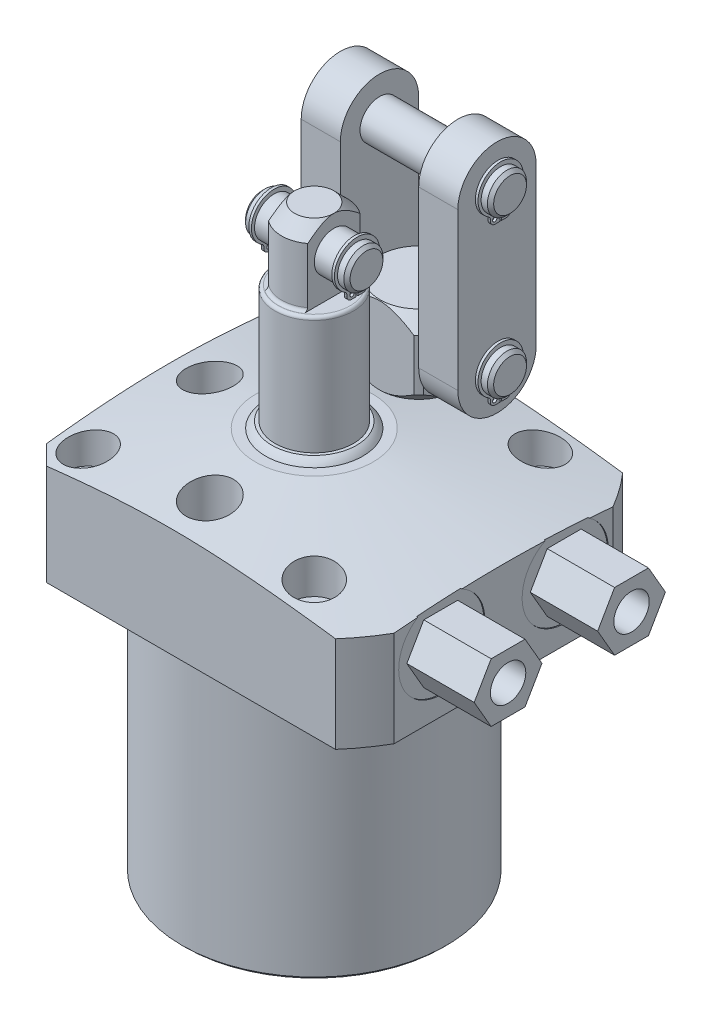
SolidWorks part; units mm, degrees
material "Alloy Steel"
ref_plane "Front Plane" through (0, 0, 0) normal (0, 0, 1) x (1, 0, 0)
ref_plane "Top Plane" through (0, 0, 0) normal (0, 1, 0) x (1, 0, 0)
ref_plane "Right Plane" through (0, 0, 0) normal (1, 0, 0) x (0, 0, -1)
sketch "Sketch28" plane through (0, 0, 0) normal (0, 0, 1) x (1, 0, 0)
  line L0 (0, 0) -> (0, 146.1857) construction
  line L1 (-14.2875, 30.1498) -> (-53.1749, 23.2929)
  line L2 (-53.1749, 23.2929) -> (-53.1749, 0)
  line L3 (-53.1749, 0) -> (-32.1437, 0)
  line L6 (-32.1437, 0) -> (-32.1437, -63.5)
  line L9 (-32.1437, -63.5) -> (0, -63.5)
  line L10 (0, -63.5) -> (0, 30.1498)
  line L11 (0, 30.1498) -> (-14.2875, 30.1498)
  dimension "D2" = 64.2874
  dimension "D3" = 63.5
  dimension "D5" = 106.3498
  dimension "D6" = 10
  dimension "D7" = 28.575
  dimension "D8" = 30.1498
revolve "Revolve7" add sketch "Sketch28" angle 360 about L0
sketch "Sketch3" plane through (0, 30.1498, 0) normal (0, 1, 0) x (-1, 0, 0)
  line L0 (34.925, -34.925) -> (-46.0248, -34.925)
  line L3 (-46.0248, 34.925) -> (34.925, 34.925)
  line L4 (34.925, -34.925) -> (34.925, 34.925)
  line L5 (-46.0248, -34.925) -> (-46.0248, 34.925)
  line L6 (-29.7523, 0) -> (31.3525, 0) construction
  dimension "D1" = 69.85
  dimension "D2" = 46.0248
  dimension "D5" = 34.925
extrude "Cut-Extrude9" cut sketch "Sketch3" against normal up to next (93.6498 mm away) flip side to cut
chamfer "Chamfer8" distance 4.7498 angle 45 2 edges at (-34.925, 11.98, -34.925) (-34.925, 11.98, 34.925)
chamfer "Chamfer5" distance 0.762 angle 45 1 edges at (0, -63.5, -32.1437)
hole_wizard "Hole1" positions "Sketch32" profile "Sketch31" legacy
sketch "Sketch32" plane through (0, 30.1498, 0) normal (0, 1, 0) x (-1, 0, 0)
  line L1 (0, 0) -> (-56.2722, 0) construction
  line L2 (0, 0) -> (0, 46.6984) construction
  point P11 (-27.4955, -27.4955)
  point P23 (-27.4955, 27.4955)
  point P25 (27.4955, -27.4955)
  point P26 (27.4955, 27.4955)
  dimension "D1" = 54.991
  dimension "D2" = 54.991
sketch "Sketch31" plane through (27.4955, 30.1498, -27.4955) normal (1, 0, 0) x (0, 0, 1)
  line L0 (0, 0) -> (0, 30.1498)
  line L1 (0, 30.1498) -> (3.5687, 30.1498)
  line L2 (3.5687, 30.1498) -> (3.5687, 11.9126)
  line L3 (3.5687, 11.9126) -> (5.5499, 11.9126)
  line L4 (5.5499, 11.9126) -> (5.5499, 0)
  line L5 (5.5499, 0) -> (0, 0)
  line L6 (0, 110) -> (0, -10) construction
  dimension "Diameter" = 7.1374
  dimension "Depth" = 30.1498
  dimension "C-Bore Diameter" = 11.0998
  dimension "C-Bore Depth" = 11.9126
sketch "Sketch34" plane through (0, 30.1498, 0) normal (0, 1, 0) x (1, 0, 0)
  line L0 (0, 0) -> (-28.6526, 0) construction
  circle A0 centre (0, 25.4) radius 5.7531
  circle A1 centre (0, -25.4) radius 5.7531
  circle A2 centre (0, 0) radius 25.4 construction
  circle A3 centre (-25.4, 0) radius 5.7531
  dimension "D1" = 11.5062
  dimension "D2" = 25.4
extrude "Cut-Extrude10" cut sketch "Sketch34" against normal blind 15.875
ref_plane "Plane23" through (0, 15.0876, 0) normal (0, -1, 0) x (1, 0, 0)
sketch "S2D0007" plane through (0, 15.0876, 0) normal (0, -1, 0) x (1, 0, 0)
  line L0 (46.0248, -15.0114) -> (46.0248, -25.4889)
  line L1 (46.0248, -25.4889) -> (45.7708, -25.4889)
  line L2 (45.7708, -25.4889) -> (45.7708, -21.228)
  line L3 (45.7708, -21.228) -> (43.7007, -20.788)
  line L4 (43.7007, -20.788) -> (42.9025, -19.9898)
  line L5 (42.9025, -19.9898) -> (31.8008, -19.9898)
  line L6 (31.8008, -19.9898) -> (28.8095, -15.0114)
  line L7 (28.8095, -15.0114) -> (46.0248, -15.0114)
  line L8 (-11.7468, -15.0114) -> (-12.1894, -15.0114) construction
  line L10 (46.0248, -26.6325) -> (46.0248, 26.6325) construction
  dimension "D1" = 12.4333
  dimension "D2" = 59
  dimension "D3" = 9.9568
  dimension "D4" = 45
  dimension "D5" = 12
  dimension "D6" = 2.0701
  dimension "D7" = 0.254
  dimension "D8" = 20.955
  dimension "D9" = 15.0114
  dimension "D10" = 13.97
revolve "Cut-Revolve2" cut sketch "S2D0007" angle 360 about L8
ref_plane "Plane24" through (0, 0, -15.0114) normal (0, 0, 1) x (1, 0, 0)
sketch "Sketch6" plane through (0, 0, -15.0114) normal (0, 0, 1) x (1, 0, 0)
  line L0 (40.0976, 0) -> (-30.1752, 0) construction
  line L1 (45.1675, 0) -> (45.1675, 1.4478)
  line L2 (45.1675, 1.4478) -> (42.1071, 1.4478)
  line L3 (40.0976, 0) -> (46.0248, 0) construction
  line L5 (39.497, 0.5588) -> (40.64, 0.5588)
  line L6 (39.497, 0) -> (45.1675, 0)
  line L8 (39.497, 0.5588) -> (39.497, 0)
  line L9 (39.497, -21.0492) -> (39.497, 0.6686) construction
  arc A1 (40.64, 0.5588) -> (42.1071, 1.4478) centre (39.497, 4.1) ccw
  dimension "D8" = 3.7211
  dimension "D1" = 1.4478
  dimension "D2" = 39.497
  dimension "D7" = 0.5588
  dimension "D9" = 11.3411
  dimension "D10" = 2.286
revolve "Cut-Revolve3" cut sketch "Sketch6" angle 360 about L9
sketch "Sketch38" plane through (45.7708, 0, 0) normal (1, 0, 0) x (0, 0, -1)
  line L1 (23.253, 15.0876) -> (19.1322, 22.225)
  line L2 (19.1322, 22.225) -> (10.8906, 22.225)
  line L3 (10.8906, 22.225) -> (6.7698, 15.0876)
  line L4 (6.7698, 15.0876) -> (10.8906, 7.9502)
  line L5 (10.8906, 7.9502) -> (19.1322, 7.9502)
  line L6 (19.1322, 7.9502) -> (23.253, 15.0876)
  circle A0 centre (15.0114, 15.0876) radius 7.1374 construction
  dimension "D1" = 14.2748
extrude "Extrude14" add sketch "Sketch38" along normal blind 16.383
hole_wizard "Hole2" positions "Sketch40" profile "Sketch39" legacy
sketch "Sketch40" plane through (62.1538, 0, 0) normal (1, 0, 0) x (0, 0, -1)
  arc A0 (10.2098, 24.4001) -> (20.8282, 23.8021) centre (15.0114, 15.0876) ccw construction
  point P0 (15.0114, 15.0876)
sketch "Sketch39" plane through (62.1538, 15.0876, -15.0114) normal (0, 1, 0) x (0, 0, -1)
  line L0 (0, 0) -> (0, 6.7056)
  line L1 (0, 6.7056) -> (4.3053, 6.7056)
  line L2 (4.3053, 6.7056) -> (4.3053, 0)
  line L3 (4.3053, 0) -> (0, 0)
  line L4 (0, 110) -> (0, -10) construction
  dimension "Diameter" = 8.6106
  dimension "Depth" = 6.7056
mirror "Mirror6" about plane through (0, 0, 0) normal (0, 0, 1) of "Hole2", "Extrude14", "Cut-Revolve2", "Cut-Revolve3"
sketch "Sketch33" plane through (0, 0, -15.0114) normal (0, 0, 1) x (1, 0, 0)
  line L0 (39.497, 8.3297) -> (39.497, -4.9597) construction
  line L1 (39.497, 2.4904) -> (39.497, -1.971) construction
  line L2 (33.8264, 1.4478) -> (45.1675, 1.4478) construction
  circle A0 centre (34.7154, 0.5842) radius 0.889
  dimension "D3" = 1.778
  dimension "D1" = 9.5631
  dimension "D2" = 0.8636
revolve "Revolve9" add sketch "Sketch33" angle 360 about L0
mirror "Mirror7" about plane through (0, 0, 0) normal (0, 0, 1) of bodies 147
sketch "Sketch12" plane through (0, 0, 0) normal (0, 0, -1) x (-1, 0, 0)
  line L0 (0, 30.1498) -> (0, 31.6738)
  line L1 (0, 31.6738) -> (10.287, 31.6738)
  line L2 (0, 30.1498) -> (11.811, 30.1498)
  line L3 (0, 22.1056) -> (0, 27.6194) construction
  line L4 (14.2875, 30.1498) -> (-14.2875, 30.1498) construction
  arc A0 (11.811, 30.1498) -> (10.287, 31.6738) centre (7.778, 27.6408) ccw
  dimension "D1" = 4.7498
  dimension "D2" = 1.524
  dimension "D3" = 20.574
  dimension "D4" = 23.622
revolve "Revolve2" add sketch "Sketch12" angle 360 about L3
ref_plane "Plane25" through (0, 0, 0) normal (-1, 0, 0) x (0, 0, 1)
sketch "Sketch13" plane through (0, 0, 0) normal (0, 0, 1) x (1, 0, 0)
  line L0 (0, 31.6738) -> (0, 77.7748)
  line L1 (0, 77.7748) -> (4.7625, 77.7748)
  line L2 (4.7625, 77.7748) -> (7.9375, 74.5998)
  line L3 (7.9375, 60.325) -> (7.9375, 74.5998)
  line L4 (9.5187, 31.6738) -> (0, 31.6738)
  line L5 (0, 23.0264) -> (0, 64.961) construction
  line L6 (-6.0362, 69.85) -> (17.7755, 69.85) construction
  line L7 (10.287, 31.6738) -> (-10.287, 31.6738) construction
  line L8 (40.0976, 0) -> (-30.1752, 0) construction
  line L10 (7.9375, 60.325) -> (9.5187, 60.325)
  line L11 (9.5187, 60.325) -> (9.5187, 31.6738)
  dimension "D1" = 7.9248
  dimension "D2" = 69.85
  dimension "D3" = 15.875
  dimension "D4" = 45
  dimension "D5" = 3.175
  dimension "D6" = 19.0373
  dimension "D7" = 17.4498
revolve "Revolve3" add sketch "Sketch13" angle 360 about L5
sketch "Sketch14" plane through (0, 77.7748, 0) normal (0, 1, 0) x (-1, 0, 0)
  line L0 (4.7625, 6.35) -> (4.7625, -6.35)
  line L2 (-4.7625, -6.35) -> (-4.7625, 6.35)
  line L4 (0, 0) -> (0, 0.0001) construction
  line L5 (0, -34.2265) -> (0, 34.2265) construction
  circle A0 centre (0, 0) radius 7.9375 construction
  arc A1 (4.7625, -6.35) -> (4.7625, 6.35) centre (0, 0) ccw
  arc A2 (-4.7625, 6.35) -> (-4.7625, -6.35) centre (0, 0) ccw
  dimension "D1" = 9.525
extrude "Cut-Extrude7" cut sketch "Sketch14" against normal up to surface (17.4498 mm away) up to face at (0, 60.325, -7.9375)
fillet "Fillet4" radius 0.762 3 edges at (0, 60.325, -9.5187) (0, 60.325, -7.9375) (0, 60.325, 7.9375)
sketch "Sketch29" plane through (0, 0, 0) normal (-1, 0, 0) x (0, 0, 1)
  line L0 (0, 77.7748) -> (-4.7625, 77.7748) construction
  circle A0 centre (0, 69.85) radius 4.7523
  dimension "D1" = 9.5047
  dimension "D2" = 7.9248
extrude "Extrude11" add sketch "Sketch29" along normal mid plane 25.4
sketch "Sketch16" plane through (-12.7, 52.3748, 0) normal (-1, 0, 0) x (0, 0, 1)
  line L0 (0.2083, 13.0097) -> (0.2083, 10.7745)
  line L1 (2.4435, 12.1667) -> (2.4435, 11.8159)
  line L2 (1.4021, 10.7745) -> (0.2083, 10.7745)
  line L3 (-2.4435, 12.1667) -> (-2.4435, 11.8159)
  line L4 (-1.4021, 10.7745) -> (-0.2083, 10.7745)
  line L5 (-0.2083, 13.0097) -> (-0.2083, 10.7745)
  line L6 (0, -3.8062) -> (0, 3.1748) construction
  arc A0 (0.2083, 13.0097) -> (-0.2083, 13.0097) centre (0, 17.4752) ccw
  arc A1 (2.9311, 13.0487) -> (-2.9311, 13.0487) centre (0, 17.7165) ccw
  arc A2 (2.9311, 13.0487) -> (2.4435, 12.1667) centre (3.4849, 12.1667) ccw
  arc A3 (1.4021, 10.7745) -> (2.4435, 11.8159) centre (1.4021, 11.8159) ccw
  circle A4 centre (1.2446, 11.8159) radius 0.5207
  arc A5 (-2.9311, 13.0487) -> (-2.4435, 12.1667) centre (-3.4849, 12.1667) cw
  arc A6 (-1.4021, 10.7745) -> (-2.4435, 11.8159) centre (-1.4021, 11.8159) cw
  circle A7 centre (-1.2446, 11.8159) radius 0.5207
  circle A8 centre (0, 17.4752) radius 4.7523 construction
  dimension "D1" = 5.5118
  dimension "D4" = 1.0414
  dimension "D6" = 1.0414
  dimension "D7" = 2.2352
  dimension "D8" = 4.4704
  dimension "D10" = 1.0414
  dimension "D11" = 1.0414
  dimension "D2" = 2.2352
  dimension "D3" = 0.2413
  dimension "D5" = 1.2446
  dimension "D9" = 0.4166
extrude "Extrude2" add sketch "Sketch16" against normal blind 0.635 from offset 2.286
chamfer "Chamfer6" distance 0.762 angle 45 2 edges at (12.7, 69.85, 4.7523) (-12.7, 69.85, 4.7523)
mirror "Mirror2" about plane through (0, 0, 0) normal (-1, 0, 0) of "Extrude2"
sketch "Sketch35" plane through (0, 0, 0) normal (-1, 0, 0) x (0, 0, 1)
  line L0 (-25.4, 43.5741) -> (-25.4, 11.6793) construction
  line L1 (-25.4, 14.2748) -> (-19.05, 14.2748)
  line L2 (-19.05, 14.2748) -> (-19.05, 30.1498)
  line L3 (-19.05, 30.1498) -> (-16.002, 30.1498)
  line L4 (-12.7, 33.4518) -> (-12.7, 45.8978)
  line L5 (-16.002, 49.1998) -> (-25.4, 49.1998)
  line L6 (-25.4, 49.1998) -> (-25.4, 14.2748)
  line L8 (-12.7, 45.8978) -> (-16.002, 49.1998)
  line L9 (-16.002, 30.1498) -> (-12.7, 33.4518)
  line L10 (26.6325, 0) -> (34.925, 0) construction
  point P6 (-12.7, 30.1498)
  point P7 (-12.7, 49.1998)
  dimension "D2" = 12.7
  dimension "D3" = 25.4
  dimension "D4" = 34.925
  dimension "D5" = 19.05
  dimension "D6" = 25.4
  dimension "D9" = 3.302
  dimension "D10" = 3.302
  dimension "D7" = 30.1498
revolve "Revolve10" add sketch "Sketch35" angle 360 about L0
sketch "Sketch36" plane through (0, 49.1998, 0) normal (0, 1, 0) x (1, 0, 0)
  line L0 (0, 25.4) -> (-25.4, 25.4) construction
  line L1 (9.525, 33.8003) -> (9.525, 16.9997)
  line L2 (8.4003, 34.925) -> (-8.4003, 34.925)
  line L3 (-9.525, 33.8003) -> (-9.525, 16.9997)
  line L4 (8.4003, 15.875) -> (-8.4003, 15.875)
  line L5 (0, 25.4) -> (0, 0) construction
  line L6 (0, 34.2265) -> (0, -34.2265) construction
  circle A0 centre (0, 25.4) radius 12.7 construction
  arc A2 (8.4003, 34.925) -> (-8.4003, 34.925) centre (0, 25.4) ccw
  arc A3 (-9.525, 33.8003) -> (-9.525, 16.9997) centre (0, 25.4) ccw
  arc A4 (9.525, 16.9997) -> (9.525, 33.8003) centre (0, 25.4) ccw
  arc A5 (-8.4003, 15.875) -> (8.4003, 15.875) centre (0, 25.4) ccw
  dimension "D1" = 19.05
  dimension "D2" = 19.05
extrude "Cut-Extrude11" cut sketch "Sketch36" against normal up to surface (19.05 mm away) up to face at (0, 30.1498, -16.002)
sketch "Sketch30" plane through (0, 0, 0) normal (-1, 0, 0) x (0, 0, 1)
  line L0 (-34.925, 0) -> (34.925, 0) construction
  circle A0 centre (-25.4, 39.6748) radius 4.7523
  dimension "D3" = 9.5047
  dimension "D1" = 39.6748
  dimension "D2" = 25.4
extrude "Extrude12" add sketch "Sketch30" along normal mid plane 44.45
sketch "Sketch19" plane through (-22.225, 11.0998, -22.225) normal (-1, 0, 0) x (0, 0, 1)
  line L0 (-2.9667, 24.1095) -> (-2.9667, 21.8743)
  line L1 (-0.7315, 23.2665) -> (-0.7315, 22.9157)
  line L2 (-1.7729, 21.8743) -> (-2.9667, 21.8743)
  line L3 (-5.6185, 23.2665) -> (-5.6185, 22.9157)
  line L4 (-4.5771, 21.8743) -> (-3.3833, 21.8743)
  line L5 (-3.3833, 24.1095) -> (-3.3833, 21.8743)
  line L6 (-3.175, -5.3833) -> (-3.175, 4.2478) construction
  arc A0 (-2.9667, 24.1095) -> (-3.3833, 24.1095) centre (-3.175, 28.575) ccw
  arc A1 (-0.2439, 24.1485) -> (-6.1061, 24.1485) centre (-3.175, 28.8163) ccw
  arc A2 (-0.2439, 24.1485) -> (-0.7315, 23.2665) centre (0.3099, 23.2665) ccw
  arc A3 (-1.7729, 21.8743) -> (-0.7315, 22.9157) centre (-1.7729, 22.9157) ccw
  circle A4 centre (-1.7221, 22.9157) radius 0.5207
  arc A5 (-6.1061, 24.1485) -> (-5.6185, 23.2665) centre (-6.6599, 23.2665) cw
  arc A6 (-4.5771, 21.8743) -> (-5.6185, 22.9157) centre (-4.5771, 22.9157) cw
  circle A7 centre (-4.6279, 22.9157) radius 0.5207
  circle A8 centre (-3.175, 28.575) radius 4.7523 construction
  dimension "D1" = 5.5118
  dimension "D3" = 0.2413
  dimension "D4" = 1.0414
  dimension "D5" = 1.0414
  dimension "D6" = 1.0414
  dimension "D9" = 4.4704
  dimension "D2" = 2.2352
  dimension "D7" = 0.4166
  dimension "D8" = 2.2352
  dimension "D10" = 1.0414
  dimension "D11" = 1.2446
extrude "Extrude4" add sketch "Sketch19" against normal blind 0.635 from offset 2.286
sketch "Sketch37" plane through (-9.525, 0, 0) normal (-1, 0, 0) x (0, 0, 1)
  line L0 (-34.925, 77.7748) -> (-34.925, 39.6748)
  line L1 (-15.875, 77.7748) -> (-15.875, 39.6748)
  arc A0 (-15.875, 77.7748) -> (-34.925, 77.7748) centre (-25.4, 77.7748) ccw
  arc A1 (-34.925, 39.6748) -> (-15.875, 39.6748) centre (-25.4, 39.6748) ccw
  dimension "D1" = 19.05
  dimension "D2" = 38.1
  dimension "D3" = 26.6076
extrude "Extrude13" add sketch "Sketch37" along normal blind 9.525
mirror "Mirror3" about plane through (0, 0, 0) normal (-1, 0, 0) of "Extrude4"
chamfer "Chamfer7" distance 0.762 angle 45 2 edges at (22.225, 39.6748, -20.6477) (-22.225, 39.6748, -20.6477)
pattern_linear "LPattern2" count 2 spacing 38.1 along (0, 1, 0) of "Extrude4", "Mirror3", "Chamfer7", "Extrude12"
mirror "Mirror8" about plane through (0, 0, 0) normal (-1, 0, 0) of "Extrude13"
